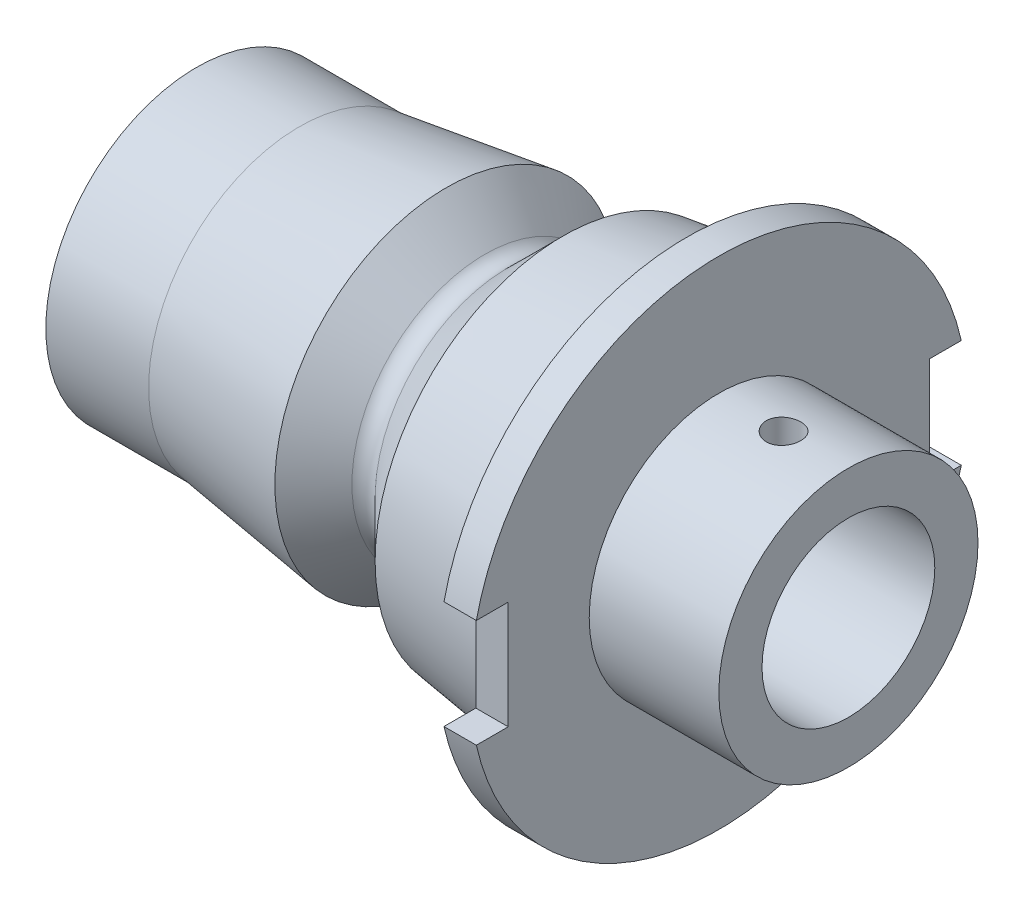
SolidWorks part; units mm, degrees
ref_plane "Front Plane" through (0, 0, 0) normal (0, 0, 1) x (1, 0, 0)
ref_plane "Top Plane" through (0, 0, 0) normal (0, 1, 0) x (1, 0, 0)
ref_plane "Right Plane" through (0, 0, 0) normal (1, 0, 0) x (0, 0, -1)
sketch "Sketch1" plane through (0, 0, 0) normal (0, 0, 1) x (1, 0, 0)
  line L0 (0, 0) -> (0, 6.982)
  line L1 (0, 6.982) -> (4.76, 6.982)
  line L2 (4.76, 6.982) -> (11.56, 7.9377)
  line L3 (11.56, 7.9377) -> (13.3431, 6.1545)
  line L4 (11.56, 7.9377) -> (23.1675, 9.569) construction
  line L5 (16.96, 8.6966) -> (22.6765, 9.5)
  line L6 (4.76, 6.982) -> (7.8351, 6.982) construction
  line L7 (11.56, 7.9377) -> (15.4875, 7.9377) construction
  line L8 (16.96, 8.6966) -> (14.4179, 6.1545)
  line L9 (16.96, 8.6966) -> (14.3792, 8.6966) construction
  line L10 (14.4179, 6.1545) -> (13.8805, 6.6919) construction
  line L11 (13.8805, 6.6919) -> (13.3431, 6.1545) construction
  line L12 (22.6765, 9.5) -> (22.6765, 11.5)
  line L13 (22.6765, 11.5) -> (24.1765, 11.5)
  line L14 (24.1765, 11.5) -> (24.1765, 0)
  line L15 (0, 0) -> (31.0457, 0) construction
  line L16 (24.1765, 0) -> (0, 0)
  line L17 (0, 0) -> (71.6905, 0) construction
  arc A0 (14.4179, 6.1545) -> (13.3431, 6.1545) centre (13.8805, 6.6919) cw
  dimension "D1" = 6.982
  dimension "D2" = 4.76
  dimension "D3" = 11.56
  dimension "D4" = 16.96
  dimension "D5" = 8
  dimension "D6" = 45
  dimension "D7" = 45
  dimension "D8" = 0.76
  dimension "D9" = 9.5
  dimension "D10" = 11.5
  dimension "D11" = 1.5
revolve "Revolve3" add sketch "Sketch1" angle 360 about L16
sketch "Sketch3" plane through (24.1765, 0, 0) normal (1, 0, 0) x (0, 0, -1)
  line L0 (0, 0) -> (15.7286, 0) construction
  line L1 (0, 0) -> (-16.4314, 0) construction
  line L2 (-11.75, 2.5) -> (-9.75, 2.5)
  line L3 (9.75, 2.5) -> (11.75, 2.5)
  line L4 (9.75, 2.5) -> (9.75, -2.5)
  line L5 (9.75, -2.5) -> (11.75, -2.5)
  line L6 (11.75, 2.5) -> (11.75, -2.5)
  line L7 (-11.75, 2.5) -> (-11.75, -2.5)
  line L8 (-11.75, -2.5) -> (-9.75, -2.5)
  line L9 (-9.75, 2.5) -> (-9.75, -2.5)
  point P8 (11.75, 0)
  point P13 (-9.75, 0)
  dimension "D1" = 2
  dimension "D2" = 5
  dimension "D3" = 9.75
  dimension "D4" = 2
  dimension "D5" = 9.75
extrude "Cut-Extrude6" cut sketch "Sketch3" against normal through all
sketch "Sketch4" plane through (24.1765, 0, 0) normal (1, 0, 0) x (0, 0, -1)
  circle A0 centre (0, 0) radius 4
  circle A1 centre (0, 0) radius 6
sketch "Sketch2" plane through (0, 0, 0) normal (1, 0, 0) x (0, 0, -1)
  circle A0 centre (0, 0) radius 2.5
  dimension "D1" = 5
extrude "Cut-Extrude7" cut sketch "Sketch2" along normal through all
extrude "Boss-Extrude1" add sketch "Sketch4" along normal blind 6
sketch "Sketch5" plane through (24.1765, 0, 0) normal (1, 0, 0) x (0, 0, -1)
  circle A0 centre (0, 0) radius 4
  dimension "D1" = 8
extrude "Cut-Extrude8" cut sketch "Sketch5" against normal blind 25
ref_plane "Plane1" through (0, 6, 0) normal (0, 1, 0) x (1, 0, 0)
hole_wizard "M2x0.4 Tapped Hole1" positions "Sketch8" profile "Sketch7" tap size "M2x0.4" standard "ANSI Metric"
sketch "Sketch8" plane through (0, 6, 0) normal (0, 1, 0) x (1, 0, 0)
  line L0 (30.1765, -6) -> (30.1765, 6) construction
  line L1 (0, 0) -> (47.7132, 0) construction
  point P0 (27.1765, 0)
  dimension "D1" = 3
sketch "Sketch7" plane through (27.1765, 6, 0) normal (1, 0, 0) x (0, 0, 1)
  line L0 (0, 0) -> (0, 2)
  line L1 (0, 2) -> (0.8, 2)
  line L2 (0.8, 2) -> (0.8, 0)
  line L5 (0.8, 0) -> (0, 0)
  line L11 (0, -6.35) -> (0, 107.95) construction
  dimension "Thru Tap Drill Dia." = 1.6
  dimension "Thru Tap Drill Depth" = 2
cosmetic thread "Hole Thread1" parameters "D2"=2
